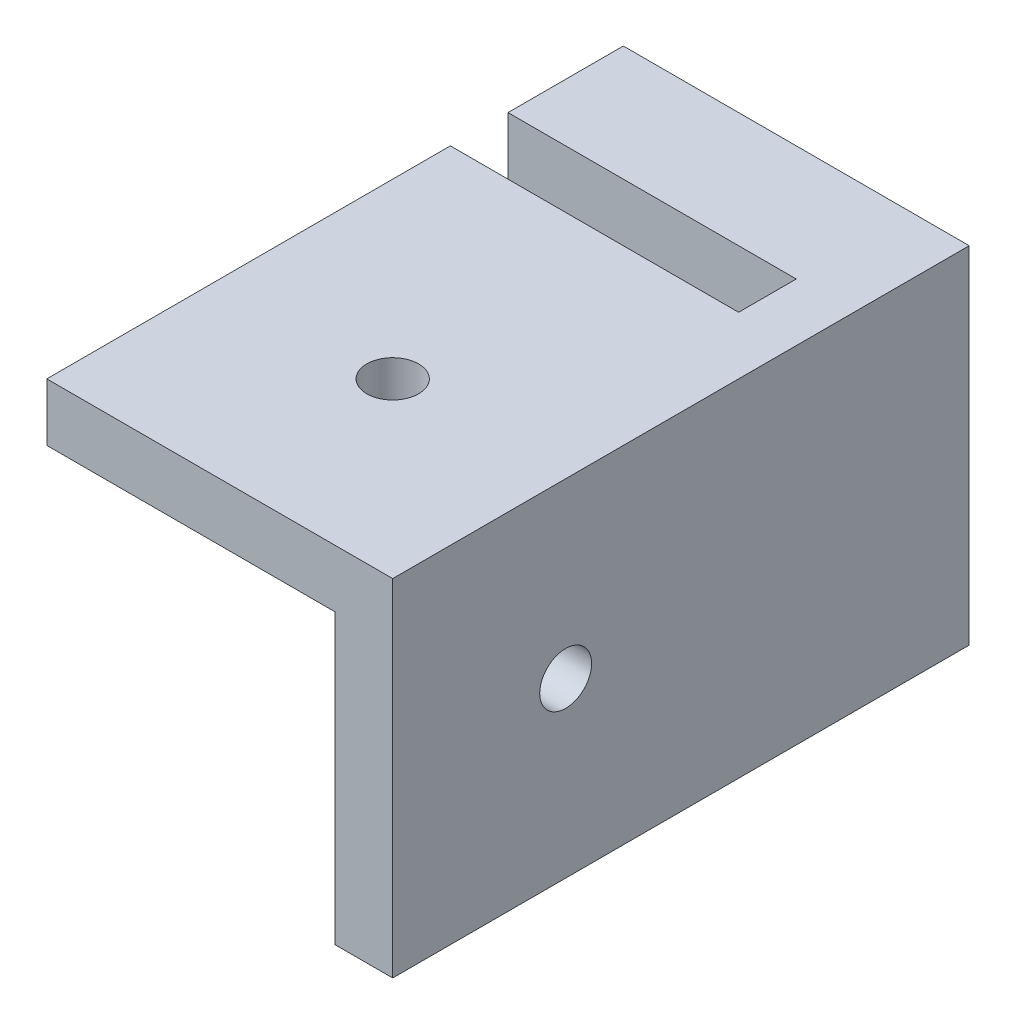
SolidWorks part; units mm, degrees
material "ABS"
ref_plane "Plano frontal" through (0, 0, 0) normal (0, 0, 1) x (1, 0, 0)
ref_plane "Plano superior" through (0, 0, 0) normal (0, 1, 0) x (1, 0, 0)
ref_plane "Plano direito" through (0, 0, 0) normal (1, 0, 0) x (0, 0, -1)
sketch "Esboço1" plane through (0, 0, 0) normal (0, 0, 1) x (1, 0, 0)
  line L9 (0, 0) -> (-30, 0)
  line L10 (0, 0) -> (0, 30)
  line L11 (0, 30) -> (-30, 30)
  line L12 (-30, 0) -> (-30, 30)
  dimension "D1" = 30
  dimension "D2" = 30
extrude "Ressalto-extrusão1" add sketch "Esboço1" along normal blind 50
sketch "Esboço2" plane through (0, 30, 0) normal (0, 1, 0) x (1, 0, 0)
  line L0 (-30, -50) -> (-30, 0) construction
  line L1 (-30, -10) -> (-5, -10)
  line L2 (-30, -10) -> (-30, -15)
  line L3 (-30, -15) -> (-5, -15)
  line L4 (-5, -10) -> (-5, -15)
  line L5 (0, 0) -> (-30, 0) construction
  line L6 (0, -50) -> (0, 0) construction
  dimension "D1" = 10
  dimension "D2" = 5
  dimension "D3" = 5
extrude "Corte-extrusão1" cut sketch "Esboço2" against normal through all
sketch "Esboço3" plane through (0, 30, 0) normal (0, 1, 0) x (1, 0, 0)
  line L0 (0, -50) -> (0, 0) construction
  line L1 (-5, -25) -> (-30, -25)
  line L2 (-5, -25) -> (-5, -50)
  line L3 (-5, -50) -> (-30, -50)
  line L4 (-30, -25) -> (-30, -50)
  line L5 (-30, -15) -> (-5, -15) construction
  dimension "D1" = 5
  dimension "D2" = 10
extrude "Corte-extrusão2" cut sketch "Esboço3" against normal through all from offset 5 offset against normal yes
hole_wizard "Furo com folga de M41" positions "3DSketch1" profile "Esboço4" hole size "M4" standard "ISO" end condition through all
sketch3d "3DSketch1"
  line L1 (-5, 0, 25) -> (-5, 25, 25) construction
  line L3 (-5, 25, 50) -> (-5, 25, 25) construction
  line L4 (-5, 25, 25) -> (-30, 25, 25) construction
  point P2 (-5, 15, 35)
  point P15 (-15, 25, 35)
  point P22 (0, 0, 0)
  dimension "D1" = 10
  dimension "D2" = 10
  dimension "D3" = 10
  dimension "D4" = 10
sketch "Esboço4" plane through (-5, 15, 35) normal (0, 1, 0) x (0, 0, 1)
  line L0 (0, 0) -> (0, 5)
  line L1 (0, 5) -> (2.25, 5)
  line L2 (2.25, 5) -> (2.25, 0)
  line L5 (2.25, 0) -> (0, 0)
  line L11 (0, -6.35) -> (0, 107.95) construction
  dimension "Thru Hole Dia." = 4.5
  dimension "Thru Hole Depth" = 5
